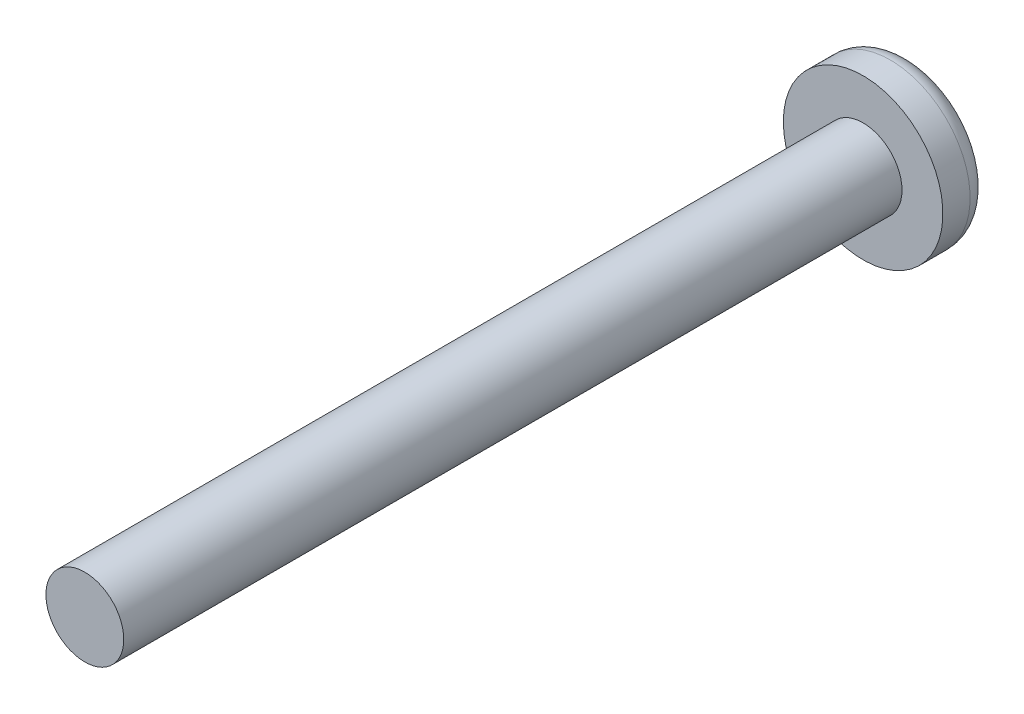
SolidWorks part; units mm, degrees
ref_plane "Piano frontale" through (0, 0, 0) normal (0, 0, 1) x (1, 0, 0)
ref_plane "Piano superiore" through (0, 0, 0) normal (0, 1, 0) x (1, 0, 0)
ref_plane "Piano destro" through (0, 0, 0) normal (1, 0, 0) x (0, 0, -1)
sketch "Schizzo1" plane through (0, 0, 0) normal (0, 0, 1) x (1, 0, 0)
  circle A0 centre (0, 0) radius 1
  dimension "D1" = 2
extrude "Estrusione-Estrusione1" add sketch "Schizzo1" along normal blind 20
sketch "Schizzo2" plane through (0, 0, 0) normal (0, 0, -1) x (-1, 0, 0)
  circle A0 centre (0, 0) radius 2.05
  dimension "D1" = 4.1
extrude "Estrusione-Estrusione2" add sketch "Schizzo2" along normal blind 1.2
fillet "Raccordo1" radius 0.5 1 edges at (-2.05, 0, -1.2)
sketch "Schizzo3" plane through (0, 0, -1.2) normal (0, 0, -1) x (-1, 0, 0)
  line L0 (0, 2.4562) -> (0, -3.0328) construction
  line L1 (-2.6308, 0) -> (3.8082, 0) construction
  line L2 (-0.25, 0.25) -> (-1, 0.25)
  line L7 (-0.25, 0.25) -> (-0.25, 1)
  line L8 (-0.25, 1) -> (0.25, 1)
  line L9 (-1, 0.25) -> (-1, -0.25)
  line L12 (1, 0.25) -> (1, -0.25)
  line L13 (0.25, 0.25) -> (0.25, 1)
  line L14 (0.25, 0.25) -> (1, 0.25)
  line L15 (0.25, -0.25) -> (1, -0.25)
  line L16 (0.25, -0.25) -> (0.25, -1)
  line L17 (-0.25, -1) -> (0.25, -1)
  line L18 (-0.25, -0.25) -> (-0.25, -1)
  line L19 (-0.25, -0.25) -> (-1, -0.25)
  dimension "D1" = 2
  dimension "D3" = 0.25
  dimension "D4" = 1
  dimension "0.25" = 0.25
extrude "Taglio-Estrusione1" cut sketch "Schizzo3" against normal blind 0.5
